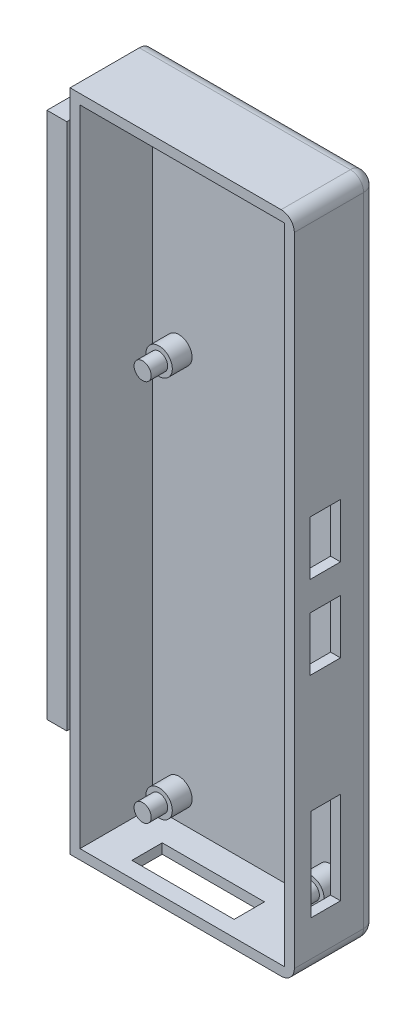
SolidWorks part; units mm, degrees
ref_plane "Plan de face" through (0, 0, 0) normal (0, 0, 1) x (1, 0, 0)
ref_plane "Plan de dessus" through (0, 0, 0) normal (0, 1, 0) x (1, 0, 0)
ref_plane "Plan de droite" through (0, 0, 0) normal (1, 0, 0) x (0, 0, -1)
sketch "Esquisse1" plane through (0, 0, 0) normal (0, 0, 1) x (1, 0, 0)
  line L1 (0, 0) -> (34, 0)
  line L2 (0, 0) -> (0, 100.65)
  line L3 (0, 100.65) -> (34, 100.65)
  line L4 (34, 0) -> (34, 100.65)
  dimension "D1" = 100.65
  dimension "D2" = 34
extrude "Boss.-Extru.1" add sketch "Esquisse1" along normal blind 12.5
sketch "Esquisse2" plane through (0, 0, 12.5) normal (0, 0, 1) x (1, 0, 0)
  line L0 (0, 100.65) -> (0, 0) construction
  line L1 (1.5, 99.15) -> (32.5, 99.15)
  line L2 (1.5, 99.15) -> (1.5, 1.5)
  line L3 (1.5, 1.5) -> (32.5, 1.5)
  line L4 (32.5, 99.15) -> (32.5, 1.5)
  line L5 (34, 0) -> (34, 100.65) construction
  line L6 (0, 0) -> (34, 0) construction
  line L7 (34, 100.65) -> (0, 100.65) construction
  dimension "D1" = 1.5
  dimension "D2" = 1.5
  dimension "D3" = 1.5
  dimension "D4" = 1.5
extrude "Enlèv. mat.-Extru.1" cut sketch "Esquisse2" against normal blind 11 contours L2 L1 L4 L3
sketch "RASP" plane through (0, 0, 1.5) normal (0, 0, 1) x (1, 0, 0)
  line L0 (1.5, 99.15) -> (1.5, 1.5) construction
  line L1 (2, 67) -> (32, 67)
  line L2 (2, 67) -> (2, 2)
  line L3 (2, 2) -> (32, 2)
  line L4 (32, 67) -> (32, 2)
  line L6 (1.5, 1.5) -> (32.5, 1.5) construction
  circle A0 centre (5.5, 5.5) radius 1.375
  circle A1 centre (28.5, 5.5) radius 1.375
  circle A2 centre (5.5, 63.5) radius 1.375
  circle A3 centre (28.5, 63.5) radius 1.375
  point P16 (32, 56)
  point P17 (32, 43.4)
  point P18 (0, 0)
  point P19 (0, 0)
  dimension "D5" = 2.75
  dimension "D6" = 2.75
  dimension "D11" = 2.75
  dimension "D12" = 2.75
  dimension "D1" = 30
  dimension "D2" = 65
  dimension "D3" = 0.5
  dimension "D4" = 0.5
  dimension "D7" = 23
  dimension "D8" = 3.5
  dimension "D9" = 3.5
  dimension "D10" = 3.5
  dimension "D13" = 23
  dimension "D14" = 3.5
  dimension "D15" = 3.5
  dimension "D16" = 3.5
  dimension "D17" = 54
  dimension "D18" = 41.4
sketch "Esquisse5" plane through (0, 0, 1.5) normal (0, 0, 1) x (1, 0, 0)
  circle A0 centre (5.5, 63.5) radius 2
  circle A1 centre (28.5, 63.5) radius 2
  circle A2 centre (5.5, 5.5) radius 2
  circle A3 centre (28.5, 5.5) radius 2
  dimension "D1" = 4
  dimension "D2" = 4
  dimension "D3" = 4
  dimension "D4" = 4
extrude "Boss.-Extru.4" add sketch "Esquisse5" along normal blind 3
sketch "Esquisse6" plane through (0, 0, 1.5) normal (0, 0, 1) x (1, 0, 0)
  circle A0 centre (5.5, 63.5) radius 1.3
  circle A1 centre (28.5, 63.5) radius 1.3
  circle A2 centre (5.5, 5.5) radius 1.3
  circle A3 centre (28.5, 5.5) radius 1.3
  dimension "D1" = 2.6
  dimension "D2" = 2.6
  dimension "D3" = 2.6
  dimension "D4" = 2.6
extrude "Boss.-Extru.5" add sketch "Esquisse6" along normal blind 5.5
fillet "Congé2" radius 2 1 edges at (34, 0, 6.25)
fillet "Congé3" radius 2 1 edges at (34, 100.65, 6.25)
fillet "Congé4" radius 2 5 edges at (16, 0, 0) (33.4142, 0.5858, 0) (16, 100.65, 0) (33.4142, 100.0642, 0) (34, 50.325, 0)
sketch "Esquisse7" plane through (0, 0, 0) normal (-1, 0, 0) x (0, 0, 1)
  line L0 (0, 98.65) -> (0, 2) construction
  line L1 (3.25, 95.45) -> (10.75, 95.45)
  line L2 (3.25, 95.45) -> (3.25, 15.45)
  line L3 (3.25, 15.45) -> (10.75, 15.45)
  line L4 (10.75, 95.45) -> (10.75, 15.45)
  line L5 (12.5, 100.65) -> (2, 100.65) construction
  dimension "D1" = 3.25
  dimension "D2" = 5.2
  dimension "D3" = 7.5
  dimension "D4" = 80
extrude "Boss.-Extru.6" add sketch "Esquisse7" along normal blind 1
sketch "Esquisse9" plane through (-1, 0, 0) normal (-1, 0, 0) x (0, 0, 1)
  line L0 (3.25, 95.45) -> (3.25, 15.45) construction
  line L1 (2, 95.45) -> (12, 95.45)
  line L2 (2, 95.45) -> (2, 15.45)
  line L3 (2, 15.45) -> (12, 15.45)
  line L4 (12, 95.45) -> (12, 15.45)
  line L5 (10.75, 95.45) -> (3.25, 95.45) construction
  dimension "D1" = 80
  dimension "D2" = 0
  dimension "D3" = 10
  dimension "D4" = 1.25
extrude "Boss.-Extru.7" add sketch "Esquisse9" along normal blind 3
sketch "Esquisse10" plane through (32.5, 0, 0) normal (-1, 0, 0) x (0, 0, 1)
  line L0 (1.5, 99.15) -> (1.5, 1.5) construction
  line L1 (10.1, 60.1) -> (5.5, 60.1)
  line L2 (10.1, 60.1) -> (10.1, 51.9)
  line L3 (10.1, 51.9) -> (5.5, 51.9)
  line L4 (5.5, 60.1) -> (5.5, 51.9)
  line L5 (10.1, 47.5) -> (5.5, 47.5)
  line L6 (10.1, 47.5) -> (10.1, 39.3)
  line L7 (10.1, 39.3) -> (5.5, 39.3)
  line L8 (5.5, 47.5) -> (5.5, 39.3)
  line L9 (10, 21.4) -> (5.5, 21.4)
  line L10 (10, 21.4) -> (10, 7.4)
  line L11 (10, 7.4) -> (5.5, 7.4)
  line L12 (5.5, 21.4) -> (5.5, 7.4)
  point P14 (0, 0)
  dimension "D1" = 4
  dimension "D2" = 4
  dimension "D3" = 4
  dimension "D4" = 14
  dimension "D5" = 8.2
  dimension "D6" = 8.2
  dimension "D7" = 4.4
  dimension "D8" = 17.9
  dimension "D9" = 4.5
  dimension "D10" = 4.6
  dimension "D11" = 4.6
  dimension "D12" = 0.6
extrude "Enlèv. mat.-Extru.2" cut sketch "Esquisse10" against normal blind 3
sketch "Esquisse11" plane through (0, 1.5, 0) normal (0, 1, 0) x (1, 0, 0)
  line L0 (1.5, -1.5) -> (32.5, -1.5) construction
  line L1 (22.4742, -10.1) -> (6.9742, -10.1)
  line L2 (22.4742, -10.1) -> (22.4742, -5.5)
  line L3 (22.4742, -5.5) -> (6.9742, -5.5)
  line L4 (6.9742, -10.1) -> (6.9742, -5.5)
  dimension "D1" = 15.5
  dimension "D2" = 4.6
  dimension "D3" = 4
extrude "Enlèv. mat.-Extru.3" cut sketch "Esquisse11" against normal blind 3 contours L2 L1 L4 L3
